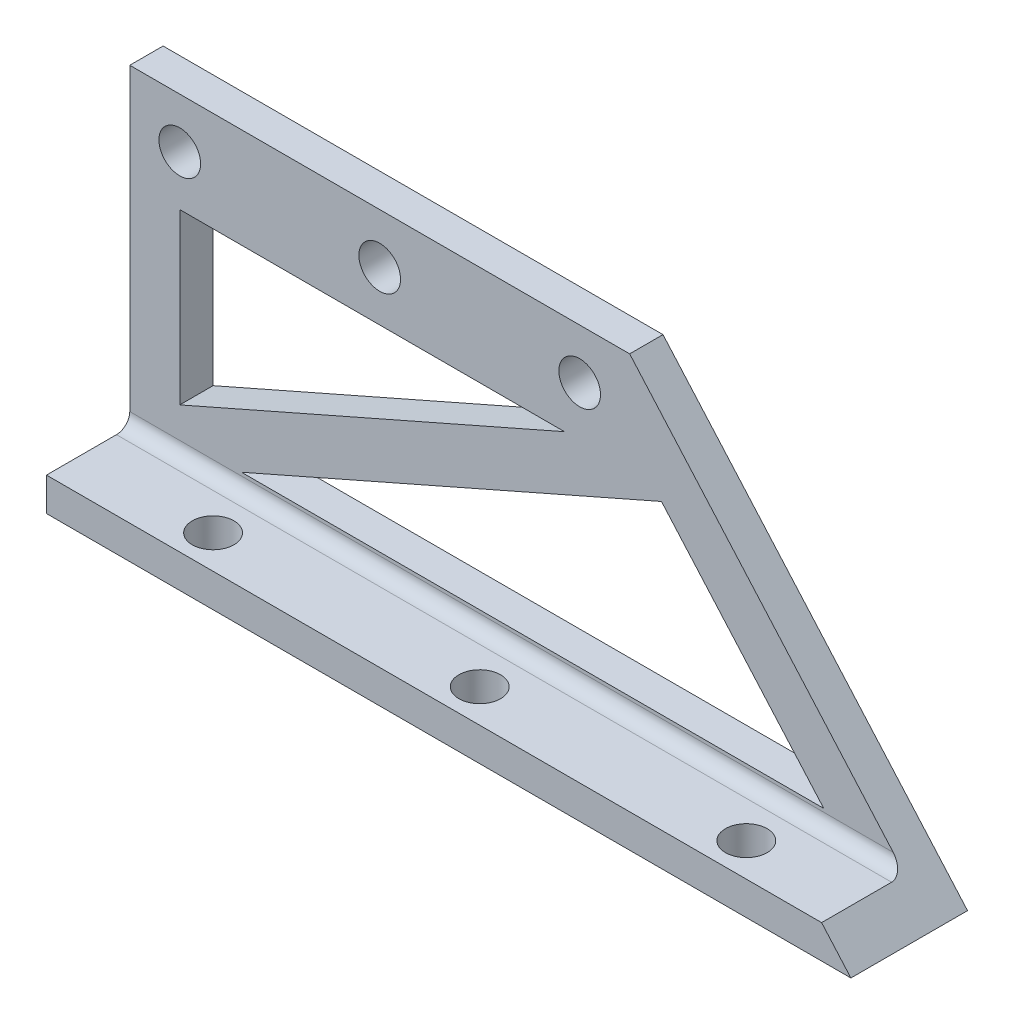
SolidWorks part; units mm, degrees
ref_plane "Front Plane" through (0, 0, 0) normal (0, 0, 1) x (1, 0, 0)
ref_plane "Top Plane" through (0, 0, 0) normal (0, 1, 0) x (1, 0, 0)
ref_plane "Right Plane" through (0, 0, 0) normal (1, 0, 0) x (0, 0, -1)
sketch "Sketch1" plane through (0, 0, 0) normal (0, 0, 1) x (1, 0, 0)
  line L0 (0, 0) -> (0, 66.04)
  line L1 (0, 66.04) -> (95.25, 66.04)
  line L2 (95.25, 66.04) -> (153.2771, 0)
  line L3 (153.2771, 0) -> (0, 0)
  line L4 (9.525, 14.7565) -> (9.525, 46.99)
  line L5 (9.525, 46.99) -> (82.83, 46.99)
  line L6 (82.83, 46.99) -> (9.525, 14.7565)
  line L7 (21.2908, 9.525) -> (101.3112, 44.7114)
  line L8 (101.3112, 44.7114) -> (132.2283, 9.525)
  line L9 (132.2283, 9.525) -> (21.2908, 9.525)
  circle A0 centre (9.525, 56.515) radius 3.9688
  circle A1 centre (47.625, 56.515) radius 3.9687
  circle A2 centre (85.725, 56.515) radius 3.9688
  dimension "D1" = 7.9375
  dimension "D2" = 38.1
  dimension "D3" = 38.1
  dimension "D4" = 9.525
  dimension "D5" = 9.525
  dimension "D6" = 9.525
  dimension "D7" = 9.525
  dimension "D8" = 9.525
  dimension "D9" = 9.525
  dimension "D10" = 56.515
  dimension "D11" = 9.525
extrude "Boss-Extrude1" add sketch "Sketch1" along normal blind 6.35
sketch "Sketch2" plane through (0, 0, 0) normal (0, -1, 0) x (1, 0, 0)
  line L0 (153.2771, 6.35) -> (153.2771, 0) construction
  line L1 (0, 6.35) -> (153.2771, 6.35)
  line L2 (0, 6.35) -> (0, 22.225)
  line L3 (0, 22.225) -> (153.2771, 22.225)
  line L4 (153.2771, 6.35) -> (153.2771, 22.225)
  circle A0 centre (25.4, 15.875) radius 3.9688
  circle A1 centre (76.2, 15.875) radius 3.9688
  circle A2 centre (127, 15.875) radius 3.9687
  dimension "D4" = 7.9375
  dimension "D1" = 50.8
  dimension "D2" = 50.8
  dimension "D3" = 15.875
  dimension "D5" = 6.35
  dimension "D6" = 25.4
extrude "Boss-Extrude2" add sketch "Sketch2" against normal blind 6.35
fillet "Fillet1" radius 2.54 1 edges
sketch "Sketch3" plane through (0, 0, 0) normal (0, 0, -1) x (-1, 0, 0)
  line L0 (-153.2771, 0) -> (-143.8777, 10.6974)
  line L1 (-153.2771, 0) -> (-95.25, 66.04) construction
  line L2 (-143.8777, 10.6974) -> (-163.562, 13.5524)
  line L3 (-163.562, 13.5524) -> (-165.2832, 4.2455)
  line L4 (-165.2832, 4.2455) -> (-153.2771, 0)
extrude "Cut-Extrude1" cut sketch "Sketch3" against normal through all
equation "\"D8@Sketch1\"=\"D6@Sketch1\""
equation "\"D9@Sketch1\"=\"D8@Sketch1\""
equation "\"D5@Sketch2\"=\"D3@Sketch2\"/2*.8"
equation "\"D10@Sketch1\"=3-0.305744in-0.469256in "
